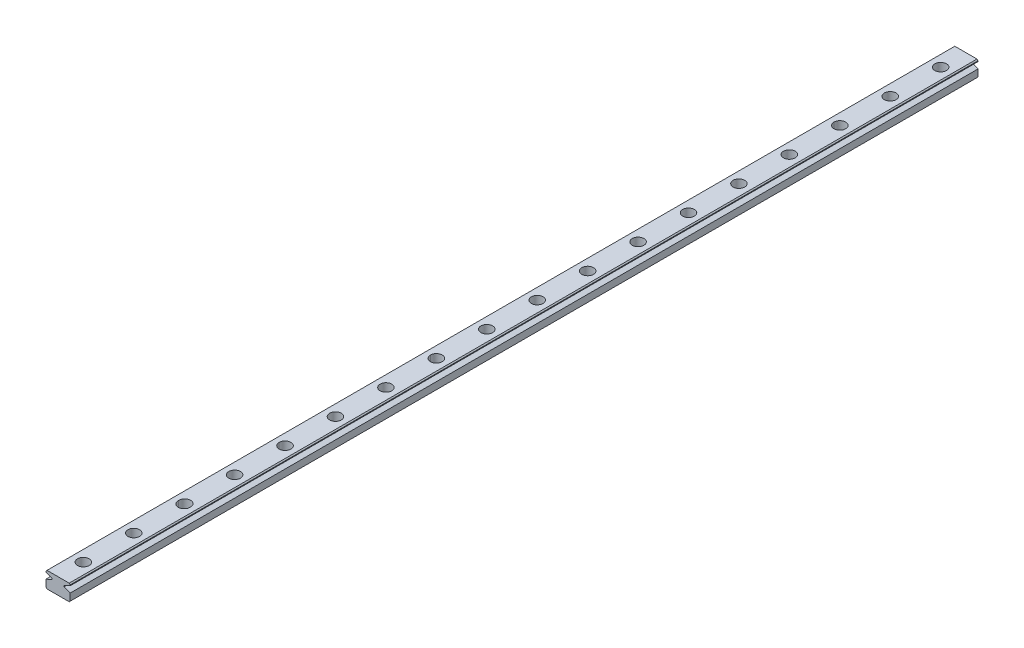
SolidWorks part; units mm, degrees
ref_plane "前视基准面" through (0, 0, 0) normal (0, 0, 1) x (1, 0, 0)
ref_plane "上视基准面" through (0, 0, 0) normal (0, 1, 0) x (1, 0, 0)
ref_plane "右视基准面" through (0, 0, 0) normal (1, 0, 0) x (0, 0, -1)
sketch "草图1" plane through (0, 0, 0) normal (0, 0, 1) x (1, 0, 0)
  line L0 (5.6176, 4.2219) -> (16.6176, 4.2219)
  line L1 (5.1176, 4.7219) -> (5.1176, 8.2219)
  line L2 (5.6176, 12.2219) -> (16.6176, 12.2219)
  line L3 (17.1176, 11.7219) -> (17.1176, 11.3434)
  line L4 (-0.6651, 7.7219) -> (23.2604, 7.7219) construction
  line L5 (8.1176, 15.7502) -> (8.1176, 0) construction
  line L6 (14.1176, 15.7502) -> (14.1176, 0) construction
  line L7 (17.1176, 8.2219) -> (14.1176, 9.4454)
  line L8 (8.1176, 9.4454) -> (5.1176, 8.2219)
  line L9 (8.1176, 9.9878) -> (8.1176, 9.4454)
  line L10 (14.1176, 9.9878) -> (17.1176, 11.3434)
  line L11 (14.1176, 9.9878) -> (14.1176, 9.4454)
  line L12 (8.1176, 9.9878) -> (5.1176, 11.2113)
  line L13 (5.1176, 11.2113) -> (5.1176, 11.7219)
  line L14 (17.1176, 8.2219) -> (17.1176, 4.7219)
  line L15 (5.1176, 11.7219) -> (5.6176, 12.2219)
  line L16 (16.6176, 12.2219) -> (17.1176, 11.7219)
  line L17 (5.6176, 4.2219) -> (5.1176, 4.7219)
  line L18 (17.1176, 4.7219) -> (16.6176, 4.2219)
  point P0 (5.1176, 4.2219)
  point P1 (17.1176, 4.2219)
  point P2 (5.1176, 12.2219)
  point P3 (17.1176, 12.2219)
  dimension "D1" = 12
  dimension "D2" = 8
  dimension "D3" = 4.5
  dimension "D4" = 3
  dimension "D5" = 3
extrude "凸台-拉伸1" add sketch "草图1" along normal blind 450
sketch "草图8" plane through (0, 12.2219, 0) normal (0, 1, 0) x (1, 0, 0)
  line L0 (11.1176, -450) -> (11.1176, 0)
  line L1 (16.6176, -450) -> (5.6176, -450) construction
  line L2 (16.6176, 0) -> (5.6176, 0) construction
sketch "草图11" plane through (0, 12.2219, 0) normal (0, 1, 0) x (1, 0, 0)
  line L0 (11.1176, -450) -> (11.1176, 0) construction
  line L1 (11.1176, -225) -> (-23.6842, -225)
  line L2 (-6.6027, -212.5) -> (21.1979, -212.5) construction
  line L3 (-6.6027, -162.5) -> (26.1227, -162.5) construction
  line L4 (-5.431, -187.5) -> (24.3933, -187.5) construction
  line L5 (-6.6027, -137.5) -> (26.1227, -137.5) construction
  line L6 (-7.9103, -112.5) -> (27.1719, -112.5) construction
  line L7 (-6.6027, -87.5) -> (27.1719, -87.5) construction
  line L8 (-7.9103, -62.5) -> (27.1719, -62.5) construction
  line L9 (-7.9103, -37.5) -> (27.1719, -37.5) construction
  line L10 (-6.6027, -237.5) -> (21.1979, -237.5) construction
  line L11 (-7.9103, -412.5) -> (27.1719, -412.5) construction
  line L12 (-7.9103, -387.5) -> (27.1719, -387.5) construction
  line L13 (-6.6027, -362.5) -> (27.1719, -362.5) construction
  line L14 (-7.9103, -337.5) -> (27.1719, -337.5) construction
  line L15 (-6.6027, -312.5) -> (26.1227, -312.5) construction
  line L16 (-6.6027, -287.5) -> (26.1227, -287.5) construction
  line L17 (-5.431, -262.5) -> (24.3933, -262.5) construction
  dimension "D1" = 25
  dimension "D2" = 12.5
  dimension "D3" = 25
  dimension "D4" = 25
  dimension "D5" = 25
  dimension "D6" = 25
  dimension "D7" = 25
  dimension "D8" = 25
sketch "草图13" plane through (0, 12.2219, 0) normal (0, 1, 0) x (1, 0, 0)
  line L0 (-10.8213, -12.5) -> (28.7847, -12.5) construction
  line L1 (-7.9103, -37.5) -> (27.1719, -37.5) construction
  line L2 (-10.8213, -437.5) -> (37.2262, -437.5) construction
  line L3 (-7.9103, -412.5) -> (27.1719, -412.5) construction
  dimension "D1" = 25
  dimension "D2" = 25
hole_wizard "孔5" positions "3D草图5" profile "草图14" legacy end condition through all
sketch3d "3D草图5"
  line L0 (11.1176, 12.2219, 450) -> (11.1176, 12.2219, 0) construction
  line L1 (-10.8213, 12.2219, 12.5) -> (28.7847, 12.2219, 12.5) construction
  line L2 (-7.9103, 12.2219, 37.5) -> (27.1719, 12.2219, 37.5) construction
  line L3 (-6.6027, 12.2219, 87.5) -> (27.1719, 12.2219, 87.5) construction
  line L4 (-7.9103, 12.2219, 112.5) -> (27.1719, 12.2219, 112.5) construction
  line L5 (-6.6027, 12.2219, 137.5) -> (26.1227, 12.2219, 137.5) construction
  line L6 (-6.6027, 12.2219, 162.5) -> (26.1227, 12.2219, 162.5) construction
  line L7 (-5.431, 12.2219, 187.5) -> (24.3933, 12.2219, 187.5) construction
  line L8 (-6.6027, 12.2219, 212.5) -> (21.1979, 12.2219, 212.5) construction
  line L9 (-6.6027, 12.2219, 237.5) -> (21.1979, 12.2219, 237.5) construction
  line L10 (-5.431, 12.2219, 262.5) -> (24.3933, 12.2219, 262.5) construction
  line L11 (-6.6027, 12.2219, 287.5) -> (26.1227, 12.2219, 287.5) construction
  line L12 (-6.6027, 12.2219, 312.5) -> (26.1227, 12.2219, 312.5) construction
  line L13 (-7.9103, 12.2219, 337.5) -> (27.1719, 12.2219, 337.5) construction
  line L14 (-6.6027, 12.2219, 362.5) -> (27.1719, 12.2219, 362.5) construction
  line L15 (-7.9103, 12.2219, 387.5) -> (27.1719, 12.2219, 387.5) construction
  line L16 (-7.9103, 12.2219, 412.5) -> (27.1719, 12.2219, 412.5) construction
  line L17 (-10.8213, 12.2219, 437.5) -> (37.2262, 12.2219, 437.5) construction
  point P0 (11.1176, 12.2219, 12.5)
  point P6 (11.1176, 12.2219, 37.5)
  point P10 (11.1176, 12.2219, 62.5044)
  point P12 (11.1176, 12.2219, 87.5)
  point P16 (11.1176, 12.2219, 112.5)
  point P20 (11.1176, 12.2219, 137.5)
  point P24 (11.1176, 12.2219, 162.5)
  point P28 (11.1176, 12.2219, 187.5)
  point P32 (11.1176, 12.2219, 212.5)
  point P36 (11.1176, 12.2219, 237.5)
  point P40 (11.1176, 12.2219, 262.5)
  point P44 (11.1176, 12.2219, 287.5)
  point P48 (11.1176, 12.2219, 312.5)
  point P52 (11.1176, 12.2219, 337.5)
  point P56 (11.1176, 12.2219, 362.5)
  point P60 (11.1176, 12.2219, 387.5)
  point P64 (11.1176, 12.2219, 412.5)
  point P68 (11.1176, 12.2219, 437.5)
sketch "草图14" plane through (11.1176, 12.2219, 12.5) normal (1, 0, 0) x (0, 0, 1)
  line L0 (0, 0) -> (0, 8)
  line L1 (0, 8) -> (1.75, 8)
  line L2 (1.75, 8) -> (1.75, 4.5)
  line L3 (1.75, 4.5) -> (2.9, 4.5)
  line L4 (2.9, 4.5) -> (2.9, 0)
  line L5 (2.9, 0) -> (0, 0)
  line L6 (0, 110) -> (0, -10) construction
  dimension "直径" = 3.5
  dimension "深度" = 8
  dimension "柱坑直径" = 5.8
  dimension "柱坑深度" = 4.5
hole_wizard "孔4" positions "3D草图4" profile "草图12" legacy end condition through all
sketch3d "3D草图4"
  line L0 (11.1176, 12.2219, 450) -> (11.1176, 12.2219, 0) construction
  line L1 (-7.9103, 12.2219, 412.5) -> (27.1719, 12.2219, 412.5) construction
  line L2 (-7.9103, 12.2219, 387.5) -> (27.1719, 12.2219, 387.5) construction
  line L3 (-7.9103, 12.2219, 337.5) -> (27.1719, 12.2219, 337.5) construction
  line L4 (-6.6027, 12.2219, 312.5) -> (26.1227, 12.2219, 312.5) construction
  line L5 (-5.431, 12.2219, 262.5) -> (24.3933, 12.2219, 262.5) construction
  line L6 (-6.6027, 12.2219, 237.5) -> (21.1979, 12.2219, 237.5) construction
  line L7 (-6.6027, 12.2219, 212.5) -> (21.1979, 12.2219, 212.5) construction
  line L8 (-5.431, 12.2219, 187.5) -> (24.3933, 12.2219, 187.5) construction
  line L9 (-6.6027, 12.2219, 162.5) -> (26.1227, 12.2219, 162.5) construction
  line L10 (-6.6027, 12.2219, 137.5) -> (26.1227, 12.2219, 137.5) construction
  line L11 (-7.9103, 12.2219, 112.5) -> (27.1719, 12.2219, 112.5) construction
  line L12 (-6.6027, 12.2219, 87.5) -> (27.1719, 12.2219, 87.5) construction
  line L13 (-7.9103, 12.2219, 62.5) -> (27.1719, 12.2219, 62.5) construction
  line L14 (-7.9103, 12.2219, 37.5) -> (27.1719, 12.2219, 37.5) construction
  point P0 (11.1176, 12.2219, 412.5)
  point P6 (11.1176, 12.2219, 387.5)
  point P10 (11.1176, 12.2219, 337.5245)
  point P12 (11.1176, 12.2219, 337.5)
  point P16 (11.1176, 12.2219, 312.5)
  point P20 (11.1176, 12.2219, 262.4995)
  point P22 (11.1176, 12.2219, 262.5)
  point P26 (11.1176, 12.2219, 237.5)
  point P30 (11.1176, 12.2219, 212.5)
  point P34 (11.1176, 12.2219, 187.5)
  point P38 (11.1176, 12.2219, 162.5)
  point P42 (11.1176, 12.2219, 137.5)
  point P46 (11.1176, 12.2219, 112.5)
  point P50 (11.1176, 12.2219, 87.5)
  point P54 (11.1176, 12.2219, 62.5)
  point P58 (11.1176, 12.2219, 37.5)
sketch "草图12" plane through (11.1176, 12.2219, 412.5) normal (1, 0, 0) x (0, 0, 1)
  line L0 (0, 0) -> (0, 8)
  line L1 (0, 8) -> (1.75, 8)
  line L2 (1.75, 8) -> (1.75, 4.5)
  line L3 (1.75, 4.5) -> (2.9, 4.5)
  line L4 (2.9, 4.5) -> (2.9, 0)
  line L5 (2.9, 0) -> (0, 0)
  line L6 (0, 110) -> (0, -10) construction
  dimension "直径" = 3.5
  dimension "深度" = 8
  dimension "柱坑直径" = 5.8
  dimension "柱坑深度" = 4.5
hole_wizard "孔3" positions "3D草图3" profile "草图9" legacy
sketch3d "3D草图3"
  line L0 (11.1176, 12.2219, 450) -> (11.1176, 12.2219, 0) construction
  point P0 (11.1176, 12.2219, 387.2239)
sketch "草图9" plane through (11.1176, 12.2219, 387.2239) normal (1, 0, 0) x (0, 0, 1)
  line L0 (0, 0) -> (0, 7.9169)
  line L1 (0, 7.9169) -> (1.75, 7.9169)
  line L2 (1.75, 7.9169) -> (1.75, 4.5)
  line L3 (1.75, 4.5) -> (2.9, 4.5)
  line L4 (2.9, 4.5) -> (2.9, 0)
  line L5 (2.9, 0) -> (0, 0)
  line L6 (0, 110) -> (0, -10) construction
  dimension "直径" = 3.5
  dimension "深度" = 8
  dimension "柱坑直径" = 5.8
  dimension "柱坑深度" = 4.5
